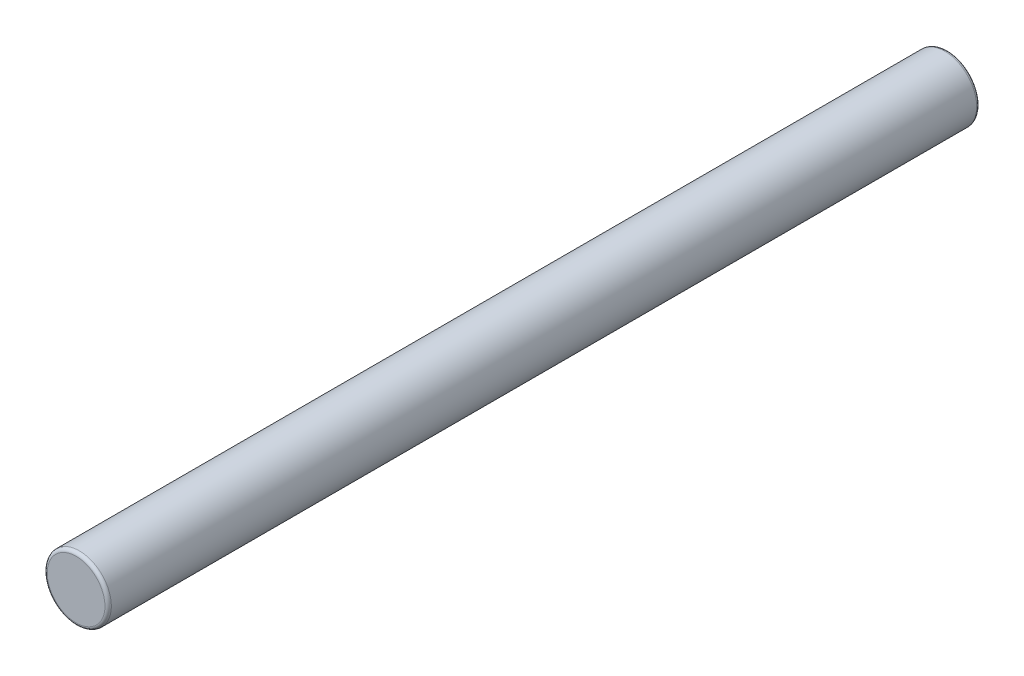
SolidWorks part; units mm, degrees
material "Acciaio inossidabile fuso"
ref_plane "Piano frontale" through (0, 0, 0) normal (0, 0, 1) x (1, 0, 0)
ref_plane "Piano superiore" through (0, 0, 0) normal (0, 1, 0) x (1, 0, 0)
ref_plane "Piano destro" through (0, 0, 0) normal (1, 0, 0) x (0, 0, -1)
sketch "Schizzo1" plane through (0, 0, 0) normal (0, 0, 1) x (1, 0, 0)
  circle A0 centre (0, 0) radius 2.5
  dimension "D1" = 5
extrude "Estrusione-Estrusione1" add sketch "Schizzo1" along normal blind 68
fillet "Raccordo1" radius 0.25 2 edges at (2.5, 0, 68) (2.5, 0, 0)
